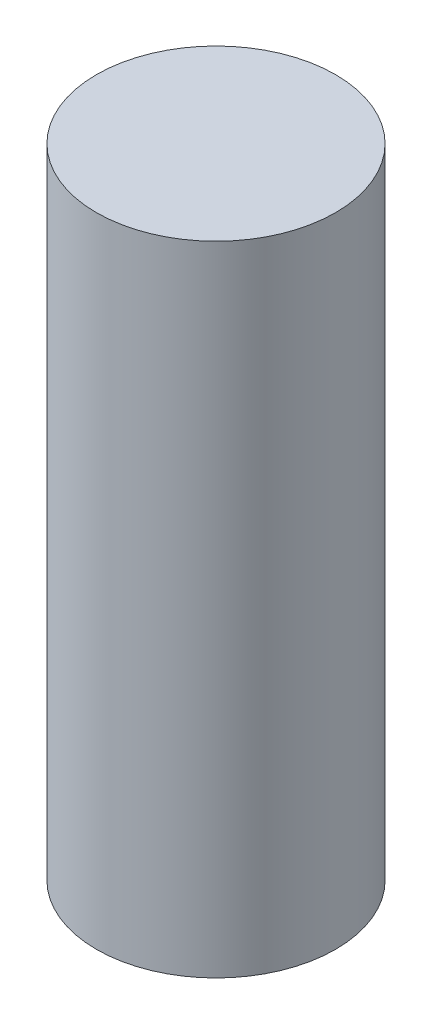
SolidWorks part; units mm, degrees
ref_plane "Front Plane" through (0, 0, 0) normal (0, 0, 1) x (1, 0, 0)
ref_plane "Top Plane" through (0, 0, 0) normal (0, 1, 0) x (1, 0, 0)
ref_plane "Right Plane" through (0, 0, 0) normal (1, 0, 0) x (0, 0, -1)
sketch "Sketch1" plane through (0, 0, 0) normal (0, 1, 0) x (1, 0, 0)
  circle A0 centre (0, 0) radius 2.38
  dimension "D1" = 4.76
extrude "dowel_body" add sketch "Sketch1" along normal blind 12.7
